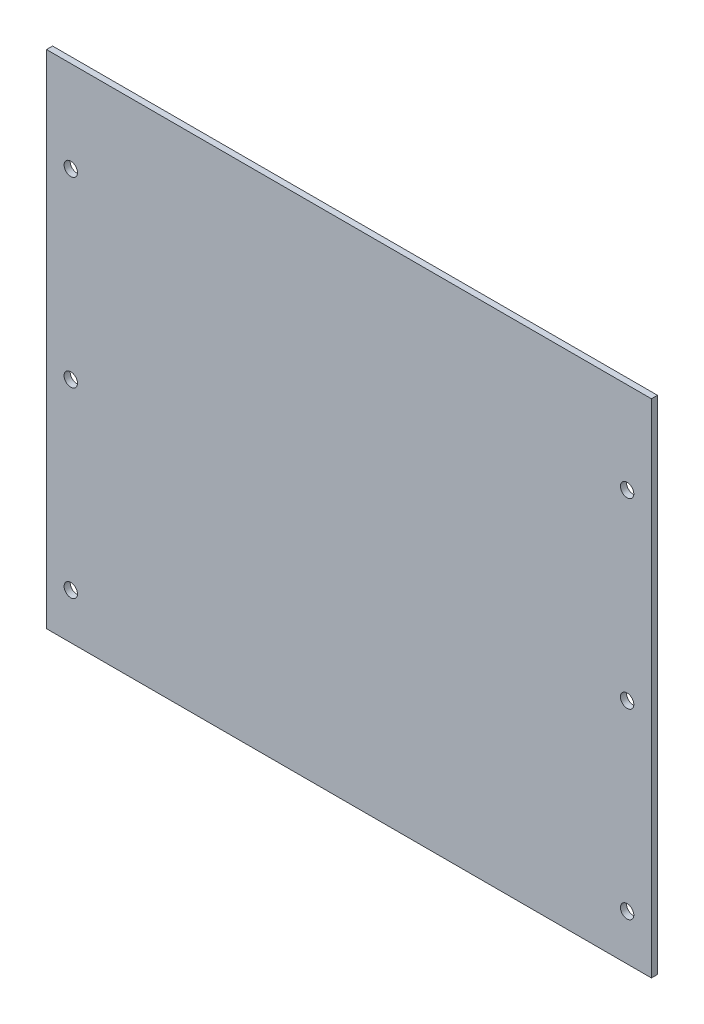
SolidWorks part; units mm, degrees
ref_plane "正面" through (0, 0, 0) normal (0, 0, 1) x (1, 0, 0)
ref_plane "平面" through (0, 0, 0) normal (0, 1, 0) x (1, 0, 0)
ref_plane "右側面" through (0, 0, 0) normal (1, 0, 0) x (0, 0, -1)
sketch "ｽｹｯﾁ1" plane through (0, 0, 0) normal (0, 0, 1) x (1, 0, 0)
  line L1 (-99.5, 82.5) -> (99.5, 82.5)
  line L2 (-99.5, 82.5) -> (-99.5, -82.5)
  line L3 (-99.5, -82.5) -> (99.5, -82.5)
  line L4 (99.5, 82.5) -> (99.5, -82.5)
  line L5 (-99.5, 82.5) -> (99.5, -82.5) construction
  line L6 (-99.5, -82.5) -> (99.5, 82.5) construction
  point P0 (0, 0)
  dimension "D1" = 199
  dimension "D2" = 165
extrude "ﾎﾞｽ - 押し出し1" add sketch "ｽｹｯﾁ1" along normal blind 2
sketch "ｽｹｯﾁ2" plane through (0, 0, 2) normal (0, 0, 1) x (1, 0, 0)
  line L0 (-99.5, -82.5) -> (-91.5, -82.5)
  line L1 (-99.5, -82.5) -> (99.5, -82.5) construction
  line L2 (-91.5, -82.5) -> (-91.5, -67.5)
  line L3 (-91.5, -82.5) -> (-91.5, -7.5)
  line L4 (-91.5, -82.5) -> (-91.5, 52.5)
  circle A0 centre (-91.5, -67.5) radius 2.2
  circle A1 centre (-91.5, -7.5) radius 2.2
  circle A2 centre (-91.5, 52.5) radius 2.2
  dimension "D5" = 4.4
  dimension "D6" = 4.4
  dimension "D7" = 4.4
  dimension "D1" = 8
  dimension "D2" = 15
  dimension "D3" = 75
  dimension "D4" = 135
extrude "ｶｯﾄ - 押し出し1" cut sketch "ｽｹｯﾁ2" against normal blind 2
sketch "ｽｹｯﾁ3" plane through (0, 0, 2) normal (0, 0, 1) x (1, 0, 0)
  line L0 (99.5, -82.5) -> (91.5, -82.5)
  line L1 (-99.5, -82.5) -> (99.5, -82.5) construction
  line L2 (91.5, -82.5) -> (91.5, -67.5)
  line L3 (91.5, -82.5) -> (91.5, -7.5)
  line L4 (91.5, -82.5) -> (91.5, 52.5)
  circle A0 centre (91.5, -67.5) radius 2.2
  circle A1 centre (91.5, -7.5) radius 2.2
  circle A2 centre (91.5, 52.5) radius 2.2
  dimension "D5" = 4.4
  dimension "D6" = 4.4
  dimension "D7" = 4.4
  dimension "D1" = 8
  dimension "D2" = 15
  dimension "D3" = 75
  dimension "D4" = 135
extrude "ｶｯﾄ - 押し出し2" cut sketch "ｽｹｯﾁ3" against normal blind 2
